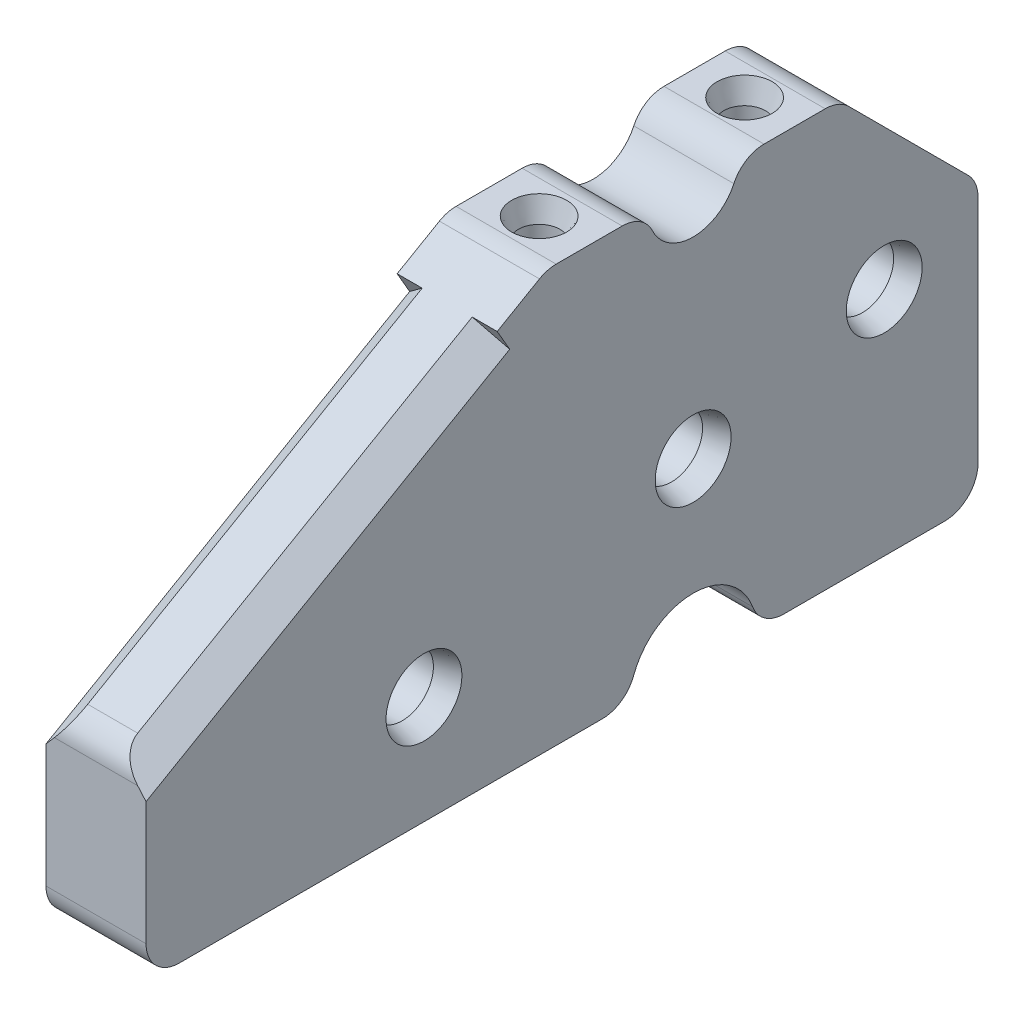
SolidWorks part; units mm, degrees
material "Oak"
ref_plane "Front Plane" through (0, 0, 0) normal (0, 0, 1) x (1, 0, 0)
ref_plane "Top Plane" through (0, 0, 0) normal (0, 1, 0) x (1, 0, 0)
ref_plane "Right Plane" through (0, 0, 0) normal (1, 0, 0) x (0, 0, -1)
sketch "Sketch1" plane through (0, 0, 0) normal (1, 0, 0) x (0, 0, -1)
  line L5 (-5.4016, 20.4227) -> (-10.4319, 20.4227)
  line L31 (21.6958, -8.7873) -> (21.6958, 8.7873)
  line L32 (20.9519, 10.5833) -> (11.8564, 19.6788)
  line L33 (10.0604, 20.4227) -> (5.4016, 20.4227)
  line L34 (-11.7019, 20.0824) -> (-40.394, 3.5171)
  line L35 (-41.664, 1.3174) -> (-41.664, -8.7873)
  line L36 (-39.124, -11.3273) -> (19.1558, -11.3273)
  arc A0 (-3.1031, 18.9636) -> (3.1031, 18.9636) centre (0, 20.4227) ccw
  arc A1 (-3.1031, 18.9636) -> (-5.4016, 20.4227) centre (-5.4016, 17.8827) ccw
  arc A2 (3.1031, 18.9636) -> (5.4016, 20.4227) centre (5.4016, 17.8827) cw
  arc A3 (11.8564, 19.6788) -> (10.0604, 20.4227) centre (10.0604, 17.8827) ccw
  arc A4 (21.6958, 8.7873) -> (20.9519, 10.5833) centre (19.1558, 8.7873) ccw
  arc A5 (19.1558, -11.3273) -> (21.6958, -8.7873) centre (19.1558, -8.7873) ccw
  arc A6 (-41.664, -8.7873) -> (-39.124, -11.3273) centre (-39.124, -8.7873) ccw
  arc A7 (-40.394, 3.5171) -> (-41.664, 1.3174) centre (-39.124, 1.3174) ccw
  arc A8 (-10.4319, 20.4227) -> (-11.7019, 20.0824) centre (-10.4319, 17.8827) ccw
  point P9 (21.6958, 0)
  point P14 (-3.429, 20.4227)
  point P19 (11.1125, 20.4227)
  point P22 (21.6958, 9.8394)
  point P26 (21.6958, -11.3273)
  point P29 (-41.664, -11.3273)
  point P32 (-41.664, 2.7838)
  point P35 (-11.1125, 20.4227)
  dimension "D7" = 6.858
  dimension "D9" = 2.54
  dimension "D3" = 21.1667
  dimension "D4" = 14.1111
  dimension "D1" = 31.75
  dimension "D2" = 45
  dimension "D5" = 30
  dimension "D6" = 22.225
  dimension "D8" = 21.6958
extrude "Boss-Extrude1" add sketch "Sketch1" along normal mid plane 7.62
sketch "Sketch2" plane through (3.81, 0, 0) normal (1, 0, 0) x (0, 0, -1)
  line L0 (21.6958, 8.1899) -> (-41.664, -8.7873) construction
  line L1 (21.6958, -8.7873) -> (21.6958, 8.7873) construction
  line L2 (-39.124, -11.3273) -> (19.1558, -11.3273) construction
  line L5 (-41.664, 1.3174) -> (-41.664, -8.7873) construction
  circle A0 centre (14.5521, 6.2758) radius 2.3813
  circle A1 centre (0, 2.3765) radius 2.3812
  circle A2 centre (-20.4973, -3.1157) radius 2.3813
  dimension "D1" = 4.7625
  dimension "D2" = 15
  dimension "D3" = 21.1667
  dimension "D4" = 7.1437
extrude "Cut-Extrude1" cut sketch "Sketch2" against normal through all
chamfer "Chamfer1" distance 0.508 angle 73 3 edges at (3.81, 6.2758, -16.9333) (3.81, 2.3765, -2.3812) (3.81, -3.1157, 18.116)
chamfer "Chamfer2" distance 0.508 angle 73 1 edges at (-3.81, -3.1157, 18.116)
chamfer "Chamfer3" distance 0.508 angle 73 1 edges at (-3.81, 2.3765, -2.3812)
chamfer "Chamfer4" distance 0.508 angle 73 1 edges at (-3.81, 6.2758, -16.9333)
sketch "Sketch3" plane through (0, 20.4227, 0) normal (0, 1, 0) x (1, 0, 0)
  line L1 (3.81, 10.0604) -> (3.81, 5.4016) construction
  line L2 (3.81, -5.4016) -> (3.81, -10.4319) construction
  circle A0 centre (0, -7.9168) radius 1.5875
  circle A1 centre (0, 7.731) radius 1.5875
  point P10 (3.81, 7.731)
  point P14 (3.81, -7.9168)
  dimension "D1" = 3.175
extrude "Cut-Extrude2" cut sketch "Sketch3" against normal blind 12.7
chamfer "Chamfer5" distance 0.508 angle 73 2 edges at (0, 20.4227, 9.5043) (0, 20.4227, -6.1435)
sketch "Sketch4" plane through (-3.81, 0, 0) normal (-1, 0, 0) x (0, 0, 1)
  line L0 (39.124, -11.3273) -> (-19.1558, -11.3273) construction
  circle A0 centre (0, -11.3273) radius 4.826
  arc A1 (-3.1031, 18.9636) -> (3.1031, 18.9636) centre (0, 20.4227) ccw construction
  point P8 (0, 16.9937)
  dimension "D1" = 9.652
extrude "Cut-Extrude3" cut sketch "Sketch4" against normal through all
fillet "Fillet1" radius 2.54 2 edges at (0, -11.3273, 4.826) (0, -11.3273, -4.826)
sketch "Sketch5" plane through (0, -11.3273, 0) normal (0, -1, 0) x (1, 0, 0)
  line L0 (3.81, -6.9142) -> (3.81, -19.1558) construction
  line L1 (3.81, -6.9142) -> (-3.81, -6.9142) construction
  line L2 (-3.81, 6.9142) -> (3.81, 6.9142) construction
  circle A0 centre (0, -13.035) radius 1.83
  circle A1 centre (0, 13.035) radius 1.8592
  point P7 (3.81, -13.035)
  dimension "D1" = 6.1208
  dimension "D2" = 6.1208
extrude "Cut-Extrude4" cut sketch "Sketch5" against normal blind 12.7
chamfer "Chamfer6" distance 0.508 angle 73 2 edges at (0, -11.3273, 11.1758) (0, -11.3273, -14.865)
ref_plane "Plane1" through (0, 0, 0) normal (0, -0.5, 0.866) x (1, 0, 0)
sketch "Sketch7" plane through (0, 0, 0) normal (0, -0.5, 0.866) x (1, 0, 0)
  line L0 (-10.16, 27.6878) -> (10.16, 27.6878)
  line L1 (10.16, 27.6878) -> (10.16, 14.9878)
  line L2 (10.16, 14.9878) -> (0, 25.1478)
  line L3 (0, 25.1478) -> (-10.16, 14.9878)
  line L4 (-10.16, 14.9878) -> (-10.16, 27.6878)
  line L5 (3.81, 23.2428) -> (-3.81, 23.2428) construction
  point P6 (0, 27.6878)
  dimension "D1" = 12.7
  dimension "D2" = 12.7
  dimension "D3" = 45
  dimension "D4" = 2.54
  dimension "D5" = 1.905
extrude "Cut-Extrude7" cut sketch "Sketch7" against normal blind 6.35 and the other way through all from offset 10.16
chamfer "Chamfer7" [suppressed] distance 1.27 angle 45
chamfer "Chamfer8" [suppressed] distance 1.27 angle 45
equation "\"D3@Sketch1\"=\"D1@Sketch1\"*2/3"
equation "\"D4@Sketch1\"=\"D3@Sketch1\"*2/3"
equation "\"D4@Sketch2\"=\"D1@Sketch2\"*1.5"
equation "\"D2@Sketch7\"=\"D1@Sketch7\""
